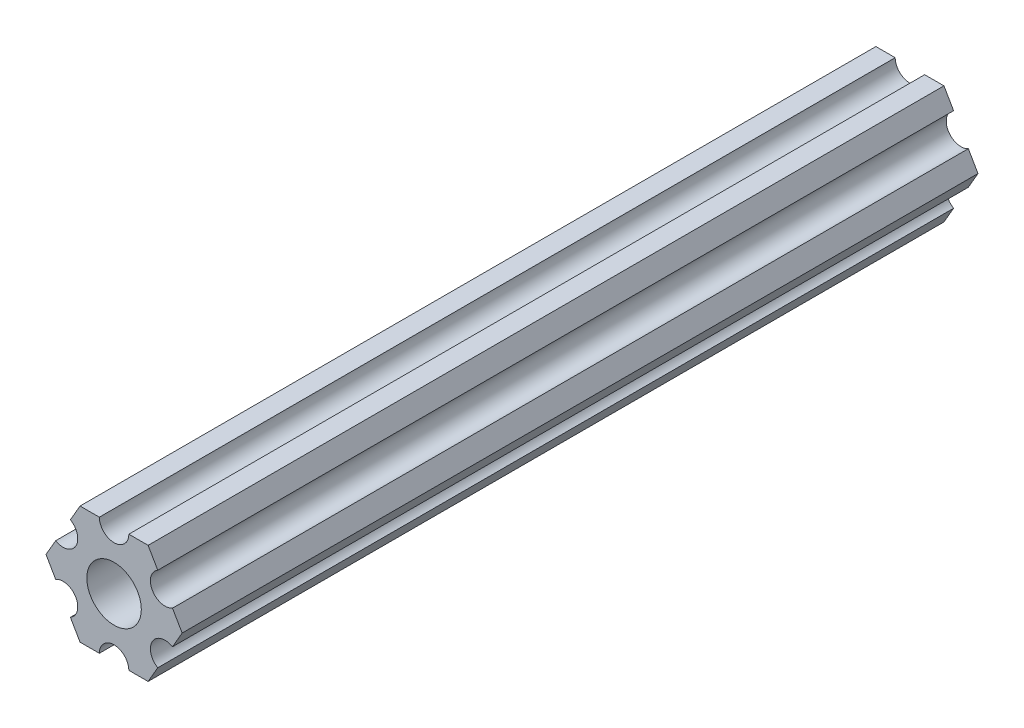
SolidWorks part; units mm, degrees
ref_plane "Front" through (0, 0, 0) normal (0, 0, 1) x (1, 0, 0)
ref_plane "Top" through (0, 0, 0) normal (0, 1, 0) x (1, 0, 0)
ref_plane "Right" through (0, 0, 0) normal (1, 0, 0) x (0, 0, -1)
ref_plane "Plane1" through (0, 0, 0) normal (0, 0, -1) x (-1, 0, 0)
sketch "Sketch1" plane through (0, 0, 0) normal (0, 0, -1) x (-1, 0, 0)
  line L0 (-4.7055, -4.5498) -> (-3.6662, -6.35)
  line L1 (-3.6662, -6.35) -> (-1.5875, -6.35)
  line L2 (1.5875, -6.35) -> (3.6662, -6.35)
  line L3 (3.6662, -6.35) -> (4.7055, -4.5498)
  line L4 (6.293, -1.8002) -> (7.3323, 0)
  line L5 (7.3323, 0) -> (6.293, 1.8002)
  line L6 (4.7055, 4.5498) -> (3.6662, 6.35)
  line L7 (3.6662, 6.35) -> (1.5875, 6.35)
  line L8 (-1.5875, 6.35) -> (-3.6662, 6.35)
  line L9 (-3.6662, 6.35) -> (-4.7055, 4.5498)
  line L10 (-6.293, 1.8002) -> (-7.3323, 0)
  line L11 (-7.3323, 0) -> (-6.293, -1.8002)
  circle A0 centre (0, 0) radius 2.9337
  arc A1 (-6.293, -1.8002) -> (-4.7055, -4.5498) centre (-5.4993, -3.175) cw
  arc A2 (-1.5875, -6.35) -> (1.5875, -6.35) centre (0, -6.35) cw
  arc A3 (4.7055, -4.5498) -> (6.293, -1.8002) centre (5.4993, -3.175) cw
  arc A4 (6.293, 1.8002) -> (4.7055, 4.5498) centre (5.4993, 3.175) cw
  arc A5 (1.5875, 6.35) -> (-1.5875, 6.35) centre (0, 6.35) cw
  arc A6 (-4.7055, 4.5498) -> (-6.293, 1.8002) centre (-5.4993, 3.175) cw
extrude "Boss-Extrude1" add sketch "Sketch1" against normal blind 85.725
